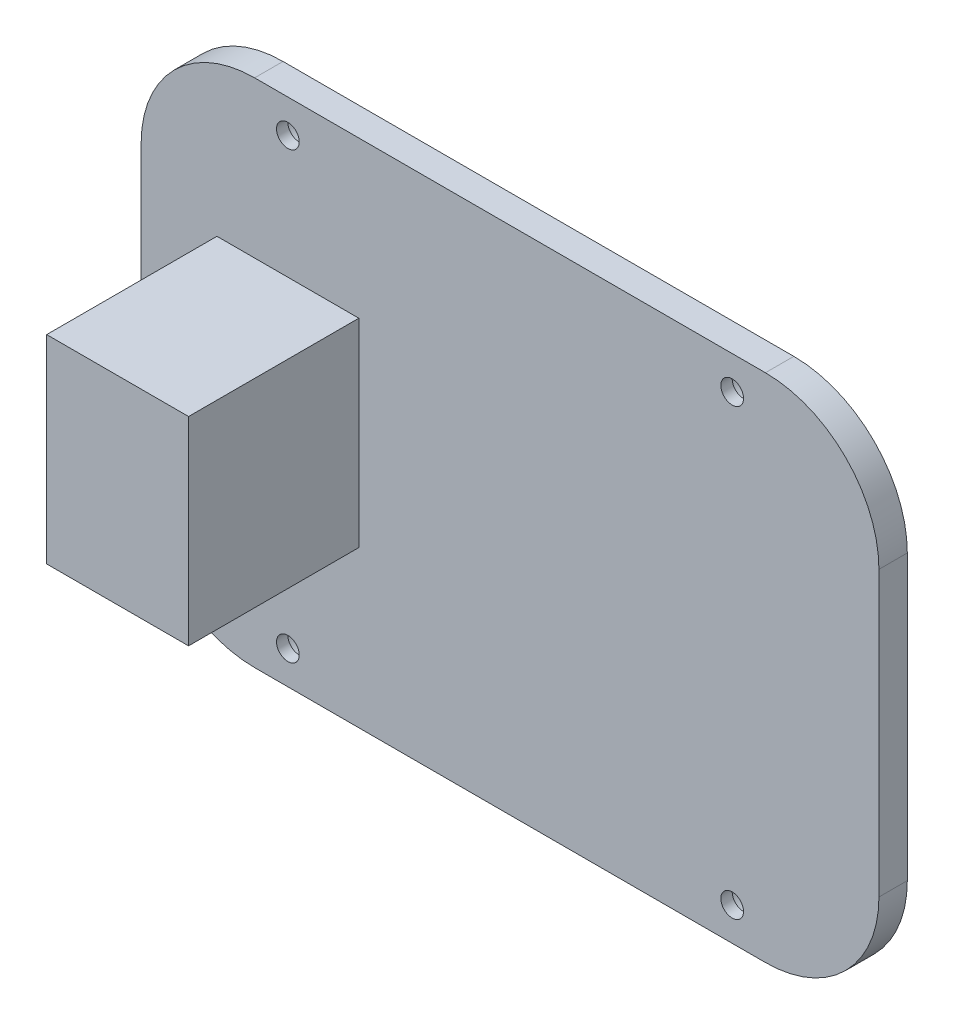
SolidWorks part; units mm, degrees
ref_plane "Front Plane" through (0, 0, 0) normal (0, 0, 1) x (1, 0, 0)
ref_plane "Top Plane" through (0, 0, 0) normal (0, 1, 0) x (1, 0, 0)
ref_plane "Right Plane" through (0, 0, 0) normal (1, 0, 0) x (0, 0, -1)
sketch "Sketch1" plane through (0, 0, 0) normal (0, 0, 1) x (1, 0, 0)
  line L1 (-65, -45) -> (65, -45)
  line L2 (-65, -45) -> (-65, 45)
  line L3 (-65, 45) -> (65, 45)
  line L4 (65, -45) -> (65, 45)
  line L5 (-65, -45) -> (65, 45) construction
  line L6 (-65, 45) -> (65, -45) construction
  point P0 (0, 0)
  dimension "D1" = 90
  dimension "D2" = 130
extrude "Boss-Extrude1" add sketch "Sketch1" along normal blind 5
fillet "Fillet1" radius 20 4 edges at (65, -45, 2.5) (-65, -45, 2.5) (65, 45, 2.5) (-65, 45, 2.5)
sketch "Sketch2" plane through (0, 0, 0) normal (0, 0, -1) x (-1, 0, 0)
  line L1 (-39.1421, -39.1421) -> (39.1421, -39.1421) construction
  line L2 (-59.1421, -19.1421) -> (-59.1421, 19.1421) construction
  line L3 (-39.1421, 39.1421) -> (39.1421, 39.1421) construction
  line L4 (59.1421, -19.1421) -> (59.1421, 19.1421) construction
  line L5 (-59.1421, -39.1421) -> (59.1421, 39.1421) construction
  line L6 (-59.1421, 39.1421) -> (59.1421, -39.1421) construction
  arc A0 (65, 25) -> (45, 45) centre (45, 25) ccw construction
  arc A1 (59.1421, 19.1421) -> (39.1421, 39.1421) centre (39.1421, 19.1421) ccw construction
  arc A2 (39.1421, -39.1421) -> (59.1421, -19.1421) centre (39.1421, -19.1421) ccw construction
  arc A3 (-39.1421, -39.1421) -> (-59.1421, -19.1421) centre (-39.1421, -19.1421) cw construction
  arc A4 (-59.1421, 19.1421) -> (-39.1421, 39.1421) centre (-39.1421, 19.1421) cw construction
  circle A5 centre (-39.1421, 39.1421) radius 4
  circle A6 centre (39.1421, 39.1421) radius 4
  circle A7 centre (-39.1421, -39.1421) radius 4
  circle A8 centre (39.1421, -39.1421) radius 4
  point P0 (0, 0)
  dimension "D1" = 20
  dimension "D2" = 8
  dimension "D3" = 8
  dimension "D4" = 8
  dimension "D5" = 8
extrude "Cut-Extrude1" cut sketch "Sketch2" against normal blind 3
sketch "Sketch3" plane through (0, 0, 0) normal (0, 0, -1) x (-1, 0, 0)
  circle A0 centre (-39.1421, 39.1421) radius 2
  circle A1 centre (39.1421, 39.1421) radius 2
  circle A2 centre (39.1421, -39.1421) radius 2
  circle A3 centre (-39.1421, -39.1421) radius 2
  dimension "D1" = 4
  dimension "D2" = 4
  dimension "D3" = 4
  dimension "D4" = 4
extrude "Cut-Extrude2" cut sketch "Sketch3" against normal through all
sketch "Sketch4" plane through (0, 0, 5) normal (0, 0, 1) x (1, 0, 0)
  line L0 (-65, 0) -> (65, 0) construction
  line L1 (-65, 25) -> (-65, -25) construction
  line L2 (65, -25) -> (65, 25) construction
  line L3 (-39.1421, 39.1421) -> (-39.1421, -39.1421) construction
  line L5 (-51.6421, -17.5) -> (-26.6421, -17.5)
  line L6 (-51.6421, -17.5) -> (-51.6421, 17.5)
  line L7 (-51.6421, 17.5) -> (-26.6421, 17.5)
  line L8 (-26.6421, -17.5) -> (-26.6421, 17.5)
  line L9 (-51.6421, -17.5) -> (-26.6421, 17.5) construction
  line L10 (-51.6421, 17.5) -> (-26.6421, -17.5) construction
  point P10 (-39.1421, 0)
  dimension "D1" = 25
  dimension "D2" = 35
extrude "Boss-Extrude2" add sketch "Sketch4" along normal blind 30
